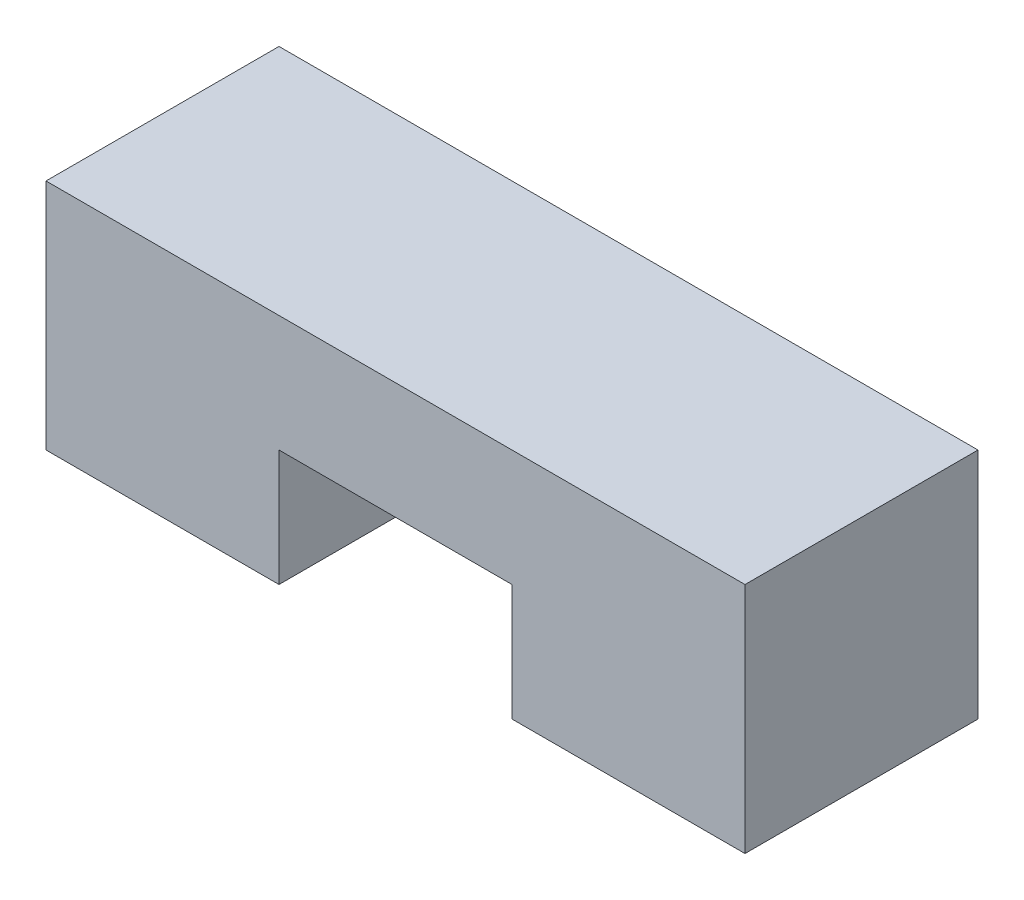
SolidWorks part; units mm, degrees
ref_plane "Front Plane" through (0, 0, 0) normal (0, 0, 1) x (1, 0, 0)
ref_plane "Top Plane" through (0, 0, 0) normal (0, 1, 0) x (1, 0, 0)
ref_plane "Right Plane" through (0, 0, 0) normal (1, 0, 0) x (0, 0, -1)
sketch "Sketch1" plane through (0, 0, 0) normal (0, 0, 1) x (1, 0, 0)
  line L0 (25.4, 0) -> (25.4, 12.7)
  line L1 (0, 0) -> (25.4, 0)
  line L2 (0, 0) -> (0, 25.4)
  line L3 (0, 25.4) -> (76.2, 25.4)
  line L4 (76.2, 0) -> (76.2, 25.4)
  line L5 (25.4, 12.7) -> (50.8, 12.7)
  line L6 (50.8, 12.7) -> (50.8, 0)
  line L7 (50.8, 0) -> (76.2, 0)
  dimension "D1" = 25.4
  dimension "D2" = 76.2
  dimension "D3" = 25.4
  dimension "D4" = 25.4
  dimension "D5" = 12.7
extrude "Boss-Extrude1" add sketch "Sketch1" against normal blind 25.4
